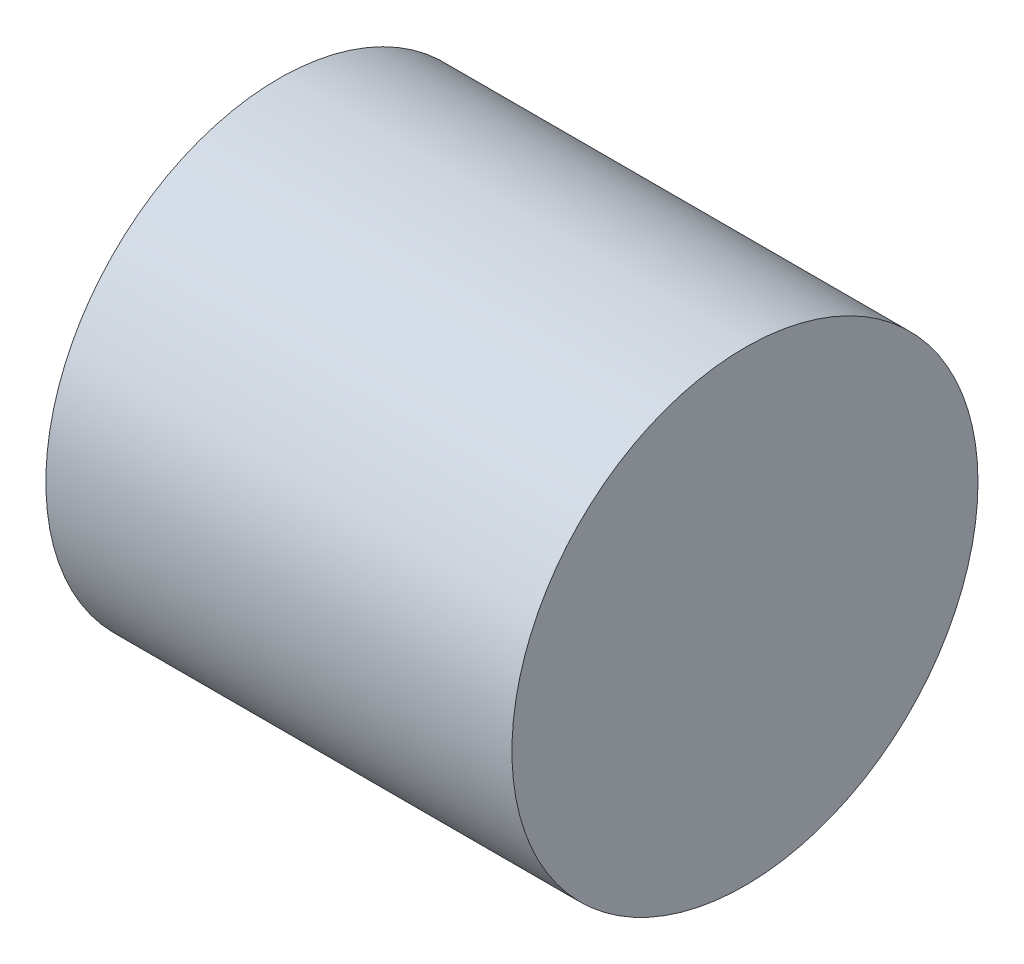
SolidWorks part; units mm, degrees
ref_plane "Front Plane" through (0, 0, 0) normal (0, 0, 1) x (1, 0, 0)
ref_plane "Top Plane" through (0, 0, 0) normal (0, 1, 0) x (1, 0, 0)
ref_plane "Right Plane" through (0, 0, 0) normal (1, 0, 0) x (0, 0, -1)
sketch "Sketch1" plane through (0, 0, 0) normal (1, 0, 0) x (0, 0, -1)
  circle A0 centre (0, 0) radius 20
  dimension "D1" = 40
extrude "Boss-Extrude2" add sketch "Sketch1" along normal blind 40
sketch "Sketch3" plane through (0, 0, 0) normal (-1, 0, 0) x (0, 0, 1)
  circle A0 centre (0, 0) radius 2
  dimension "D1" = 4
extrude "Cut-Extrude1" cut sketch "Sketch3" against normal blind 5
